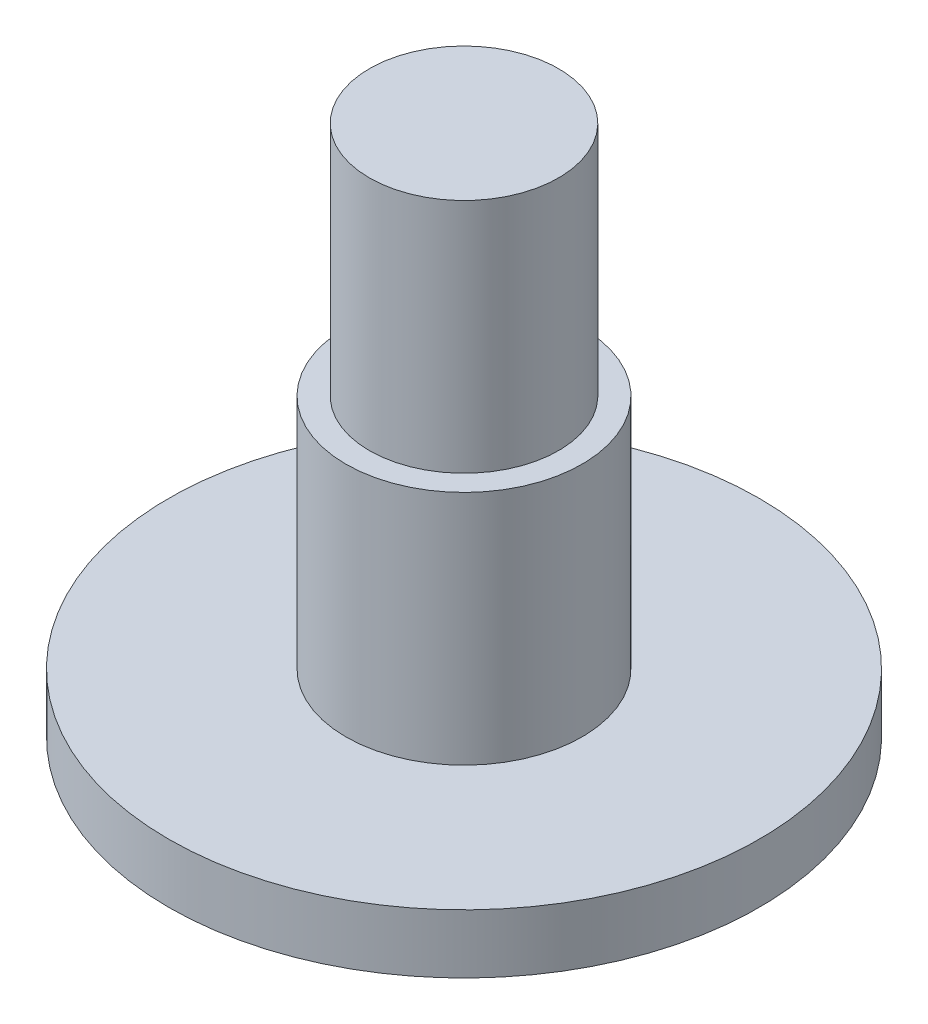
SolidWorks part; units mm, degrees
ref_plane "Front Plane" through (0, 0, 0) normal (0, 0, 1) x (1, 0, 0)
ref_plane "Top Plane" through (0, 0, 0) normal (0, 1, 0) x (1, 0, 0)
ref_plane "Right Plane" through (0, 0, 0) normal (1, 0, 0) x (0, 0, -1)
sketch "Sketch1" plane through (0, 0, 0) normal (0, 1, 0) x (1, 0, 0)
  circle A0 centre (0, 0) radius 5
  dimension "D1" = 10
extrude "Boss-Extrude1" add sketch "Sketch1" along normal blind 1
sketch "Sketch2" plane through (0, 1, 0) normal (0, 1, 0) x (1, 0, 0)
  circle A0 centre (0, 0) radius 2
  dimension "D1" = 4
extrude "Boss-Extrude2" add sketch "Sketch2" along normal blind 4
sketch "Sketch3" plane through (0, 5, 0) normal (0, 1, 0) x (1, 0, 0)
  circle A0 centre (0, 0) radius 1.6025
  dimension "D1" = 3.205
extrude "Boss-Extrude3" add sketch "Sketch3" along normal blind 4
